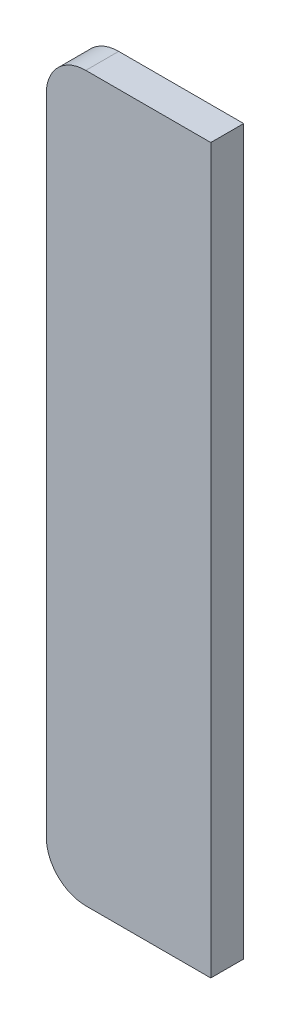
SolidWorks part; units mm, degrees
ref_plane "Front Plane" through (0, 0, 0) normal (0, 0, 1) x (1, 0, 0)
ref_plane "Top Plane" through (0, 0, 0) normal (0, 1, 0) x (1, 0, 0)
ref_plane "Right Plane" through (0, 0, 0) normal (1, 0, 0) x (0, 0, -1)
sketch "Sketch1" plane through (0, 0, 0) normal (0, 0, 1) x (1, 0, 0)
  line L1 (0, 0) -> (125, 0)
  line L2 (0, 0) -> (0, 550)
  line L3 (0, 550) -> (125, 550)
  line L4 (125, 0) -> (125, 550)
  dimension "D1" = 125
  dimension "D2" = 550
extrude "Boss-Extrude1" add sketch "Sketch1" along normal blind 25
fillet "Fillet4" radius 30 1 edges at (0, 550, 12.5)
fillet "Fillet5" radius 30 1 edges at (0, 0, 12.5)
